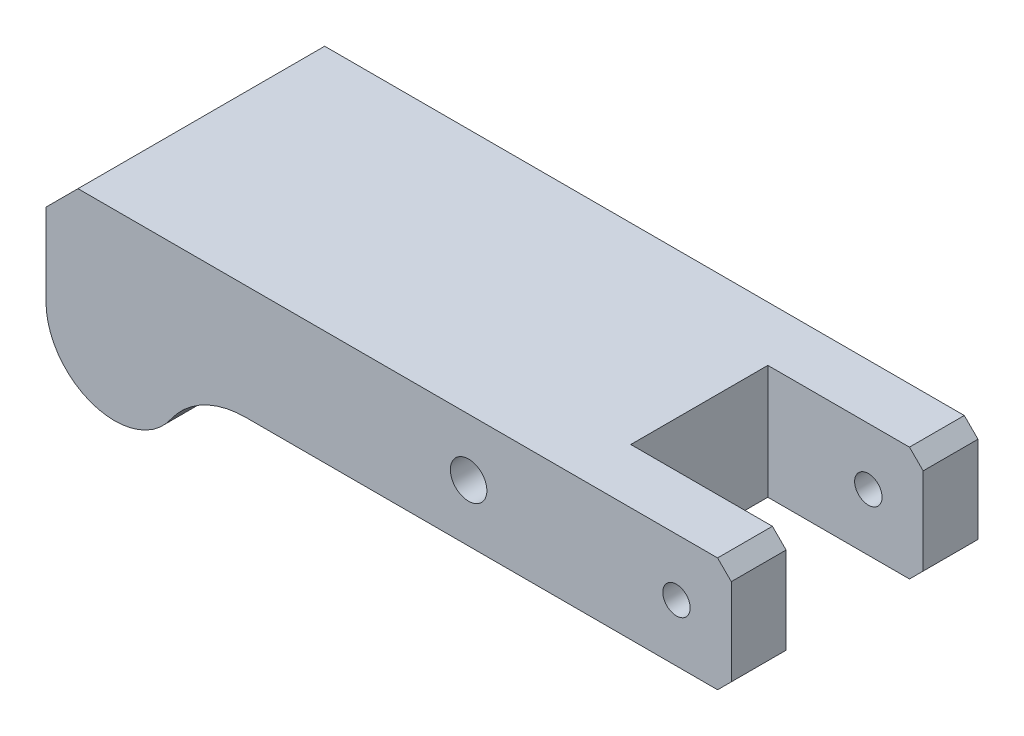
SolidWorks part; units mm, degrees
ref_plane "Front Plane" through (0, 0, 0) normal (0, 0, 1) x (1, 0, 0)
ref_plane "Top Plane" through (0, 0, 0) normal (0, 1, 0) x (1, 0, 0)
ref_plane "Right Plane" through (0, 0, 0) normal (1, 0, 0) x (0, 0, -1)
sketch "Sketch1" plane through (0, 0, 0) normal (0, 0, 1) x (1, 0, 0)
  line L0 (-59.5982, 18) -> (-52.5982, 25)
  line L1 (-52.5982, 25) -> (87.4018, 25)
  line L2 (-59.5982, 18) -> (-59.5982, 0)
  line L3 (-15.8754, 0) -> (87.4018, 0)
  line L4 (90.4018, 22) -> (90.4018, 3)
  line L5 (87.4018, 25) -> (90.4018, 22)
  line L6 (87.4018, 0) -> (90.4018, 3)
  arc A0 (-59.5982, 0) -> (-32.2884, -8.5714) centre (-44.5982, 0) ccw
  arc A1 (-32.2884, -8.5714) -> (-15.8754, 0) centre (-15.8754, -20) cw
  circle A2 centre (78.4018, 12.5) radius 3
  circle A3 centre (32.9018, 12.5) radius 4
  point P0 (-59.5982, 25)
  point P1 (90.4018, 0)
  point P3 (90.4018, 25)
  dimension "D3" = 30
  dimension "D4" = 20
  dimension "D5" = 6
  dimension "D14" = 8
  dimension "D1" = 150
  dimension "D2" = 25
  dimension "D6" = 12
  dimension "D7" = 12.5
  dimension "D8" = 7
  dimension "D9" = 45
  dimension "D10" = 3
  dimension "D11" = 45
  dimension "D12" = 3
  dimension "D13" = 45
  dimension "D15" = 45.5
extrude "Boss-Extrude1" add sketch "Sketch1" along normal blind 54
sketch "Sketch2" plane through (0, 25, 0) normal (0, 1, 0) x (1, 0, 0)
  line L0 (90.4018, -54) -> (90.4018, 0) construction
  line L1 (90.4018, -12) -> (56.4018, -12)
  line L2 (90.4018, -12) -> (90.4018, -42)
  line L3 (90.4018, -42) -> (56.4018, -42)
  line L4 (56.4018, -12) -> (56.4018, -42)
  line L5 (87.4018, 0) -> (-52.5982, 0) construction
  line L6 (87.4018, -54) -> (-52.5982, -54) construction
  dimension "D1" = 12
  dimension "D2" = 12
  dimension "D3" = 34
extrude "Cut-Extrude1" cut sketch "Sketch2" against normal blind 54
